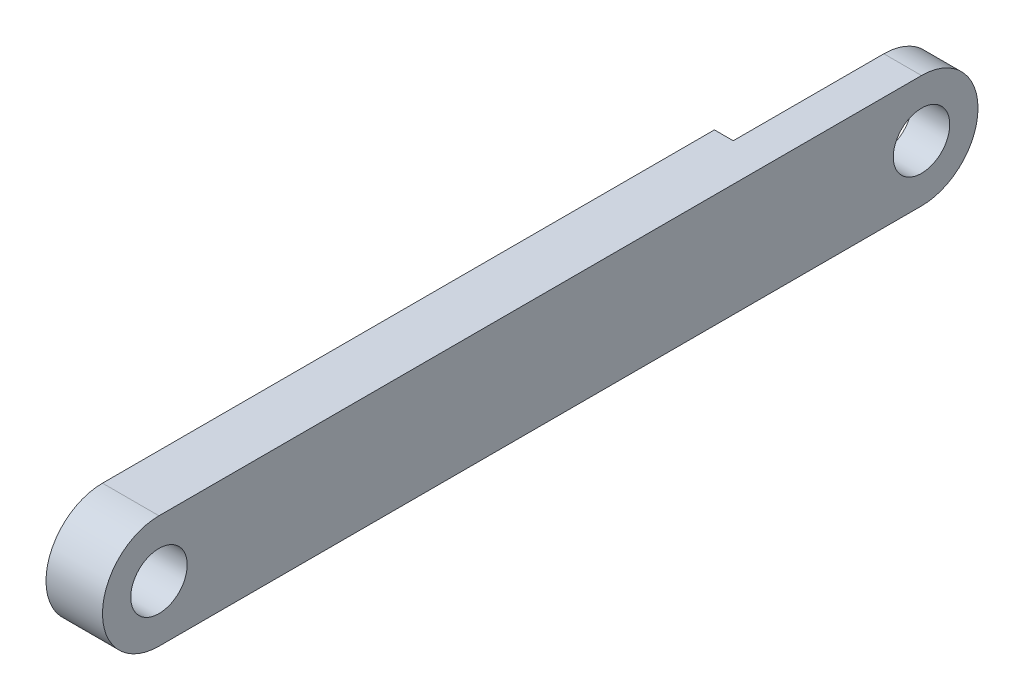
SolidWorks part; units mm, degrees
material "Plain Carbon Steel"
ref_plane "Front Plane" through (0, 0, 0) normal (0, 0, 1) x (1, 0, 0)
ref_plane "Top Plane" through (0, 0, 0) normal (0, 1, 0) x (1, 0, 0)
ref_plane "Right Plane" through (0, 0, 0) normal (1, 0, 0) x (0, 0, -1)
sketch "Sketch1" plane through (0, 0, 0) normal (1, 0, 0) x (0, 0, -1)
  line L24 (0, 3) -> (40.5, 3)
  line L25 (0, -3) -> (40.5, -3)
  arc A6 (0, 3) -> (0, -3) centre (0, 0) ccw
  arc A8 (40.5, 3) -> (40.5, -3) centre (40.5, 0) cw
  circle A10 centre (0, 0) radius 1.5
  circle A11 centre (40.5, 0) radius 1.5
  dimension "D1" = 6
  dimension "D2" = 40.5
  dimension "D3" = 3
extrude "Boss-Extrude1" add sketch "Sketch1" along normal blind 3
sketch "Sketch3" plane through (0, 0, 0) normal (-1, 0, 0) x (0, 0, 1)
  line L0 (-43.5, 3) -> (-32.5, 3)
  line L1 (-40.5, 3) -> (0, 3) construction
  line L2 (-32.5, 3) -> (-32.5, -3)
  line L3 (0, -3) -> (-40.5, -3) construction
  line L4 (-32.5, -3) -> (-43.5, -3)
  line L5 (-43.5, -3) -> (-43.5, 3)
  arc A1 (-40.5, 3) -> (-40.5, -3) centre (-40.5, 0) ccw construction
  dimension "D1" = 11
extrude "Cut-Extrude2" cut sketch "Sketch3" against normal blind 1
